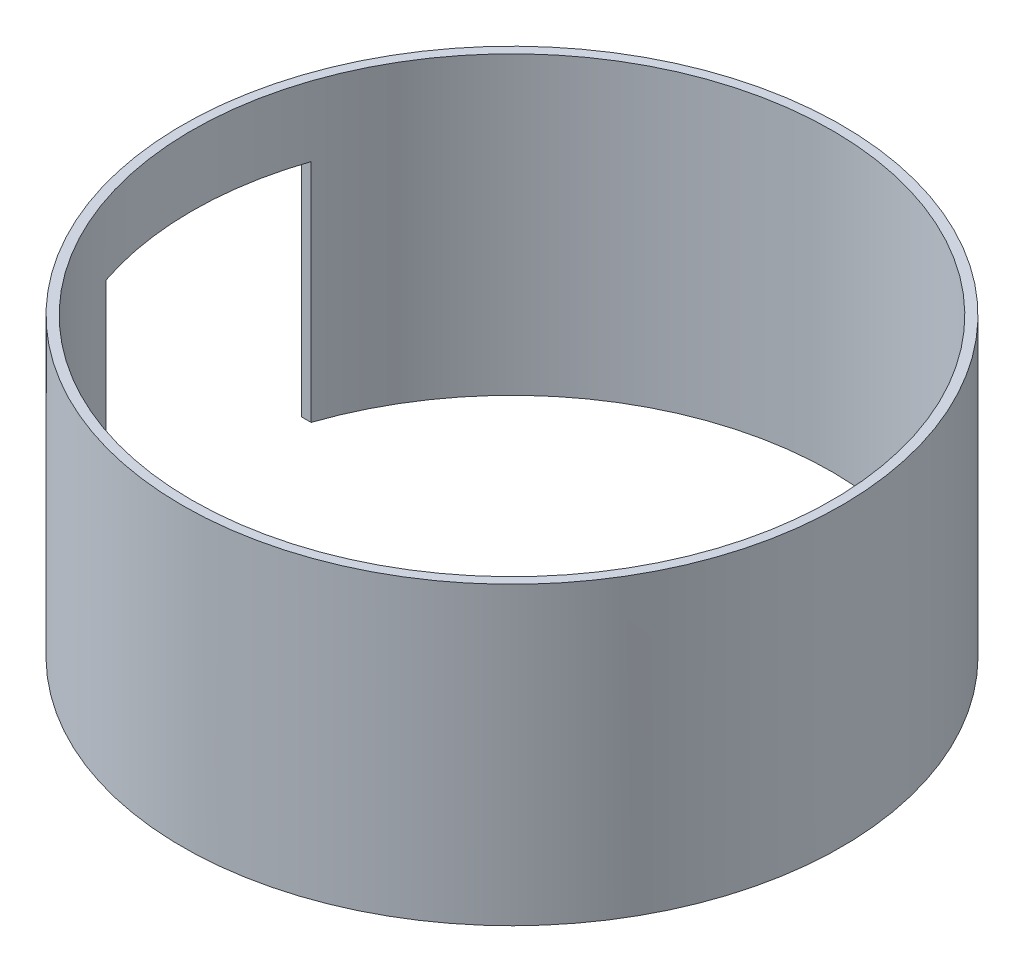
SolidWorks part; units mm, degrees
ref_plane "Front Plane" through (0, 0, 0) normal (0, 0, 1) x (1, 0, 0)
ref_plane "Top Plane" through (0, 0, 0) normal (0, 1, 0) x (1, 0, 0)
ref_plane "Right Plane" through (0, 0, 0) normal (1, 0, 0) x (0, 0, -1)
sketch "Sketch1" plane through (0, 0, 0) normal (0, 1, 0) x (1, 0, 0)
  circle A0 centre (0, 0) radius 34.375
  circle A1 centre (0, 0) radius 35.375
  dimension "D1" = 68.75
  dimension "D2" = 1
extrude "Boss-Extrude1" add sketch "Sketch1" along normal blind 31.75
sketch "Sketch2" plane through (0, 0, 0) normal (1, 0, 0) x (0, 0, -1)
  line L0 (-35.375, 0) -> (35.375, 0) construction
  line L1 (11, 24.25) -> (-11, 24.25)
  line L2 (11, 24.25) -> (11, 0)
  line L3 (11, 0) -> (-11, 0)
  line L4 (-11, 24.25) -> (-11, 0)
  line L5 (11, 24.25) -> (-11, 0) construction
  line L6 (11, 0) -> (-11, 24.25) construction
  line L7 (35.375, 31.75) -> (-35.375, 31.75) construction
  point P4 (0, 12.125)
  dimension "D1" = 22
  dimension "D3" = 7.5
extrude "Cut-Extrude1" cut sketch "Sketch2" against normal blind 43
